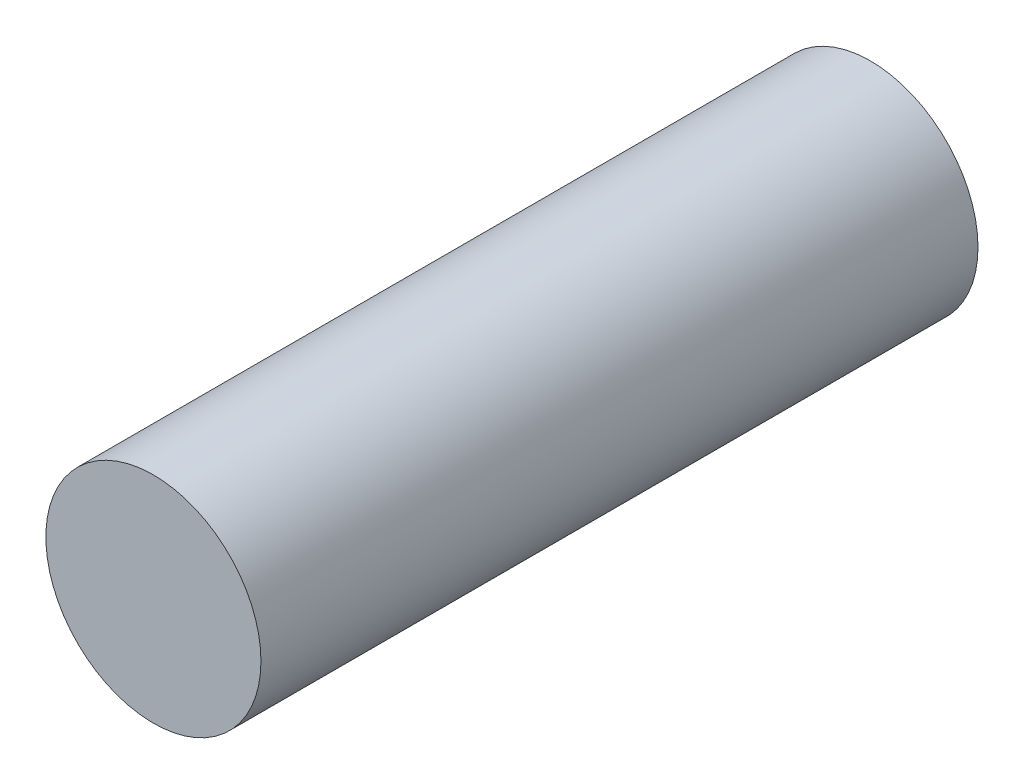
SolidWorks part; units mm, degrees
ref_plane "Front Plane" through (0, 0, 0) normal (0, 0, 1) x (1, 0, 0)
ref_plane "Top Plane" through (0, 0, 0) normal (0, 1, 0) x (1, 0, 0)
ref_plane "Right Plane" through (0, 0, 0) normal (1, 0, 0) x (0, 0, -1)
sketch "Sketch2" plane through (0, 0, 650) normal (0, 0, 1) x (1, 0, 0)
  circle A0 centre (129857.7223, -224046.5343) radius 75
  circle A1 centre (129857.7223, -224046.5343) radius 75 construction
  dimension "D2" = 150
  dimension "D1" = 0
extrude "Boss-Extrude1" add sketch "Sketch2" against normal blind 500
